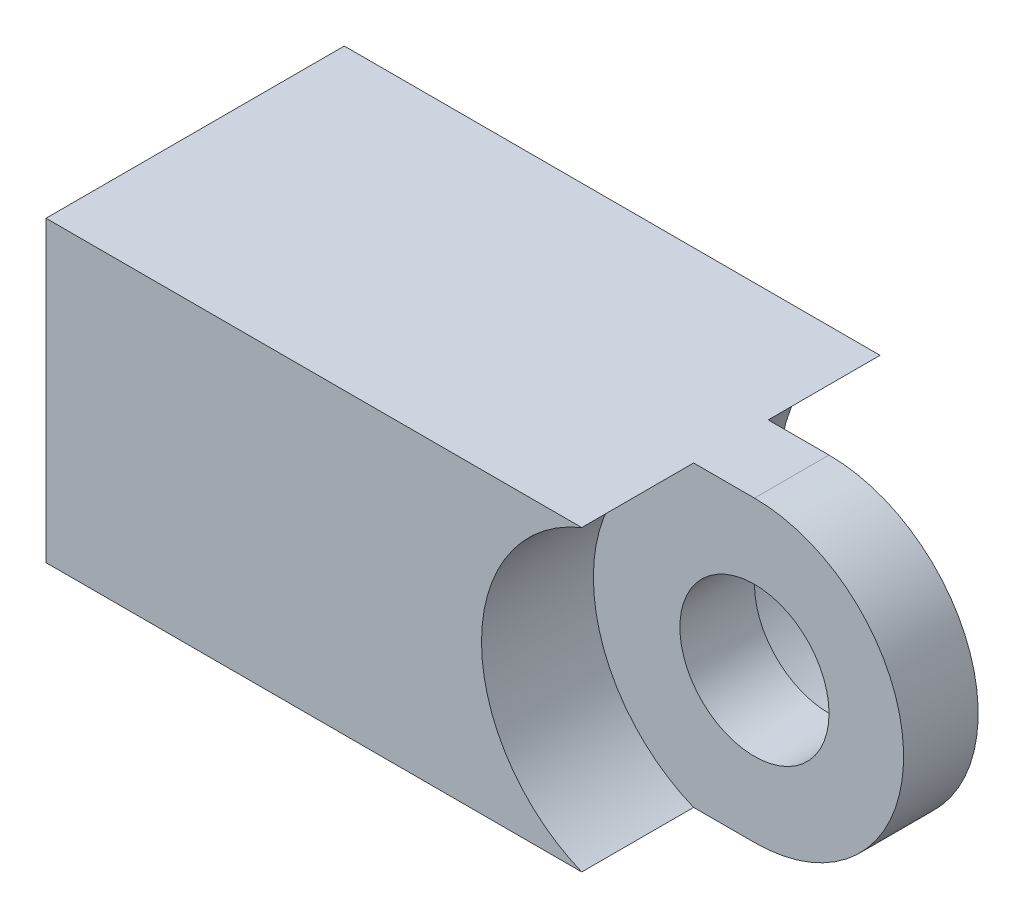
SolidWorks part; units mm, degrees
material "Free-Cutting Brass, UNS C36000"
ref_plane "Front Plane" through (0, 0, 0) normal (0, 0, 1) x (1, 0, 0)
ref_plane "Top Plane" through (0, 0, 0) normal (0, 1, 0) x (1, 0, 0)
ref_plane "Right Plane" through (0, 0, 0) normal (1, 0, 0) x (0, 0, -1)
sketch "Sketch2" plane through (0, 0, 0) normal (0, 0, 1) x (1, 0, 0)
  line L0 (0, 3.175) -> (0, -3.175) construction
  line L5 (-6.35, 3.175) -> (0, 3.175)
  line L6 (-6.35, 3.175) -> (-6.35, -3.175)
  line L7 (-6.35, -3.175) -> (0, -3.175)
  line L9 (-6.35, 3.175) -> (0, 0) construction
  line L10 (-6.35, -3.175) -> (0, 0) construction
  arc A0 (0, 3.175) -> (0, -3.175) centre (0, 0) cw
  point P0 (0, 0)
  dimension "D3" = 3.175
  dimension "D1" = 6.35
  dimension "D2" = 6.35
extrude "Boss-Extrude2" add sketch "Sketch2" along normal mid plane 1.5875
ref_plane "Plane1" through (3.175, 0, 0) normal (1, 0, 0) x (0, 0, -1)
sketch "Sketch4" plane through (-6.35, 0, 0) normal (-1, 0, 0) x (0, 0, 1)
  line L1 (-3.175, 3.175) -> (3.175, 3.175)
  line L2 (-3.175, 3.175) -> (-3.175, -3.175)
  line L3 (-3.175, -3.175) -> (3.175, -3.175)
  line L4 (3.175, 3.175) -> (3.175, -3.175)
  line L5 (-3.175, 3.175) -> (3.175, -3.175) construction
  line L6 (-3.175, -3.175) -> (3.175, 3.175) construction
  point P0 (0, 0)
  dimension "D1" = 6.35
extrude "Boss-Extrude3" add sketch "Sketch4" along normal blind 6.35
sketch "Sketch10" plane through (0, 0, 0) normal (0, 0, 1) x (1, 0, 0)
  line L0 (-6.35, -3.175) -> (0, -3.175) construction
  line L1 (-6.35, 3.175) -> (-3.175, 3.175)
  line L2 (-6.35, 3.175) -> (-6.35, -3.175)
  line L3 (-6.35, -3.175) -> (-3.175, -3.175)
  line L4 (-3.175, 3.175) -> (-3.175, -3.175) construction
  line L5 (0, 3.175) -> (-6.35, 3.175) construction
  line L6 (-3.175, 3.175) -> (-1.2952, 3.175)
  line L7 (-1.2952, -3.175) -> (-3.175, -3.175)
  line L9 (-6.35, 3.175) -> (-6.35, -3.175) construction
  line L10 (0, 3.175) -> (-6.35, 3.175) construction
  circle A0 centre (0, 0) radius 3.175 construction
  arc A1 (0, -3.175) -> (0, 3.175) centre (0, 0) ccw construction
  arc A2 (0, -3.175) -> (0, 3.175) centre (0, 0) cw construction
  arc A3 (-1.2952, -3.175) -> (-1.2952, 3.175) centre (0, 0) cw
  arc A4 (0, -3.429) -> (0, 3.429) centre (0, 0) cw construction
  point P10 (-3.175, 0)
  point P23 (0, 0)
  dimension "D1" = 0.254
extrude "Boss-Extrude4" add sketch "Sketch10" along normal mid plane 6.35
hole_wizard "#4-40 Tapped Hole3" positions "Sketch5" profile "Sketch6" tap size "#4-40" standard "ANSI Inch"
sketch "Sketch5" plane through (-12.7, 0, 0) normal (-1, 0, 0) x (0, 0, 1)
  point P0 (0, 0)
sketch "Sketch6" plane through (-12.7, 0, 0) normal (0, 1, 0) x (0, 0, 1)
  line L0 (0, 0) -> (0, 9.1882)
  line L1 (0, 9.1882) -> (1.1303, 8.509)
  line L2 (1.1303, 8.509) -> (1.1303, 0)
  line L5 (1.1303, 0) -> (0, 0)
  line L10 (0, 9.1882) -> (-1.1303, 8.509) construction
  line L11 (0, -6.35) -> (0, 107.95) construction
  dimension "Tap Drill Dia." = 2.2606
  dimension "Tap Drill Depth" = 8.509
  dimension "Drill Angle" = 118
cosmetic thread "Hole Thread1" parameters "D1"=5.6896, "D2"=2.8448
hole_wizard "1/8 (0.125) Diameter Hole1" positions "Sketch9" profile "Sketch8" hole size "1/8" standard "ANSI Inch" end condition up to next
sketch "Sketch9" plane through (0, 0, 0.7937) normal (0, 0, 1) x (1, 0, 0)
  point P0 (0, 0)
sketch "Sketch8" plane through (0, 0, 0.7937) normal (1, 0, 0) x (0, -1, 0)
  line L0 (0, 0) -> (0, 1.5875)
  line L1 (0, 1.5875) -> (1.5875, 1.5875)
  line L2 (1.5875, 1.5875) -> (1.5875, 0)
  line L5 (1.5875, 0) -> (0, 0)
  line L11 (0, -6.35) -> (0, 107.95) construction
  dimension "Thru Hole Dia." = 3.175
  dimension "Thru Hole Depth" = 1.5875
